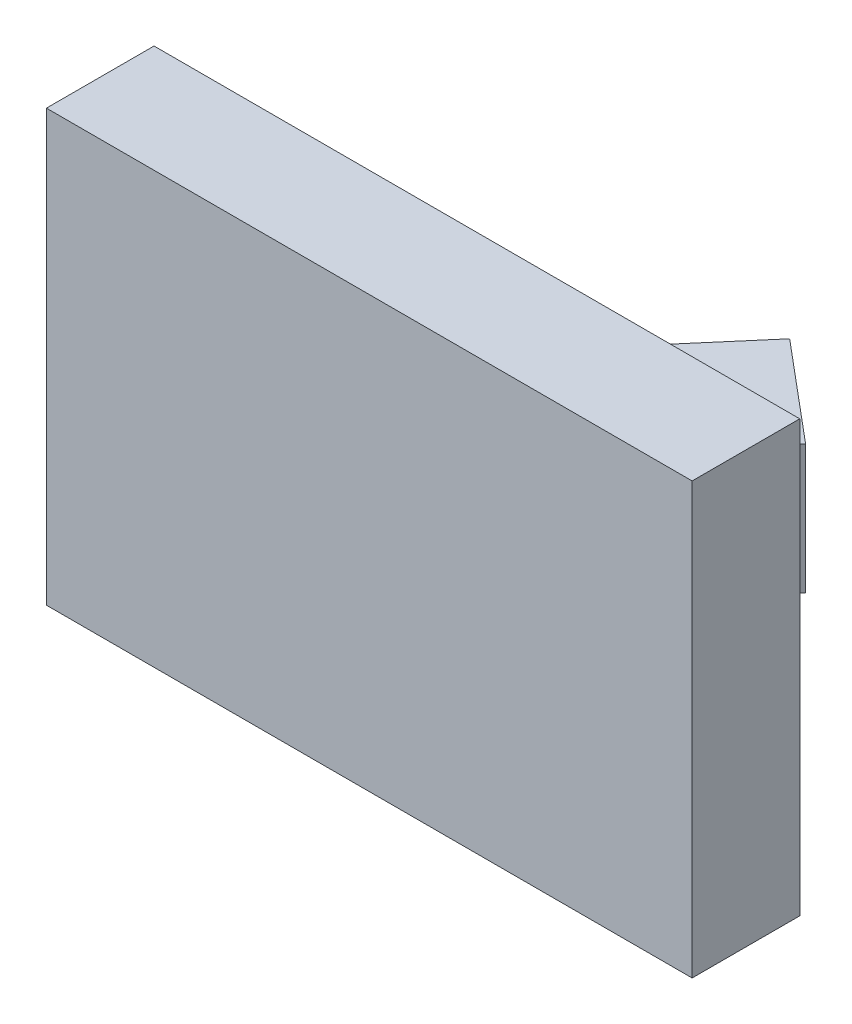
SolidWorks part; units mm, degrees
ref_plane "Alzado" through (0, 0, 0) normal (0, 0, 1) x (1, 0, 0)
ref_plane "Planta" through (0, 0, 0) normal (0, 1, 0) x (1, 0, 0)
ref_plane "Vista lateral" through (0, 0, 0) normal (1, 0, 0) x (0, 0, -1)
sketch "Croquis1" plane through (0, 0, 0) normal (0, 0, 1) x (1, 0, 0)
  line L1 (-15, 10) -> (15, 10)
  line L2 (-15, 10) -> (-15, -10)
  line L3 (-15, -10) -> (15, -10)
  line L4 (15, 10) -> (15, -10)
  line L5 (-15, 10) -> (15, -10) construction
  line L6 (-15, -10) -> (15, 10) construction
  point P0 (0, 0)
  dimension "D1" = 30
  dimension "D2" = 20
extrude "Saliente-Extruir1" add sketch "Croquis1" along normal blind 5 contours L1 L4 L3 L2
sketch "Croquis2" plane through (0, 0, 0) normal (0, 0, -1) x (-1, 0, 0)
  circle A0 centre (0, 0) radius 6
  dimension "D1" = 12
sketch "Croquis3" plane through (0, 0, 0) normal (0, 1, 0) x (1, 0, 0)
  line L0 (-4, 0) -> (4, 0)
  line L1 (4, 0) -> (9.1423, 6.1284)
  line L2 (-4, 0) -> (4.546, 9.9851)
  line L3 (0, 0) -> (0, 11.2347)
  line L4 (9.1423, 6.1284) -> (4.546, 9.9851)
  line L5 (-15, 0) -> (15, 0) construction
  point P4 (0, 0)
  dimension "D1" = 8
  dimension "D2" = 8
  dimension "D3" = 50
  dimension "D4" = 6
extrude "Saliente-Extruir2" add sketch "Croquis3" along normal blind 3 and the other way blind 3 contours L1 L4 L2 L3 L0
sketch "Croquis4" plane through (6.795, 0, -8.098) normal (0.6428, 0, -0.766) x (-0.766, 0, -0.6428)
  circle A0 centre (0, 0) radius 2.1
  dimension "D1" = 4.2
extrude "Cortar-Extruir1" cut sketch "Croquis4" against normal blind 7
